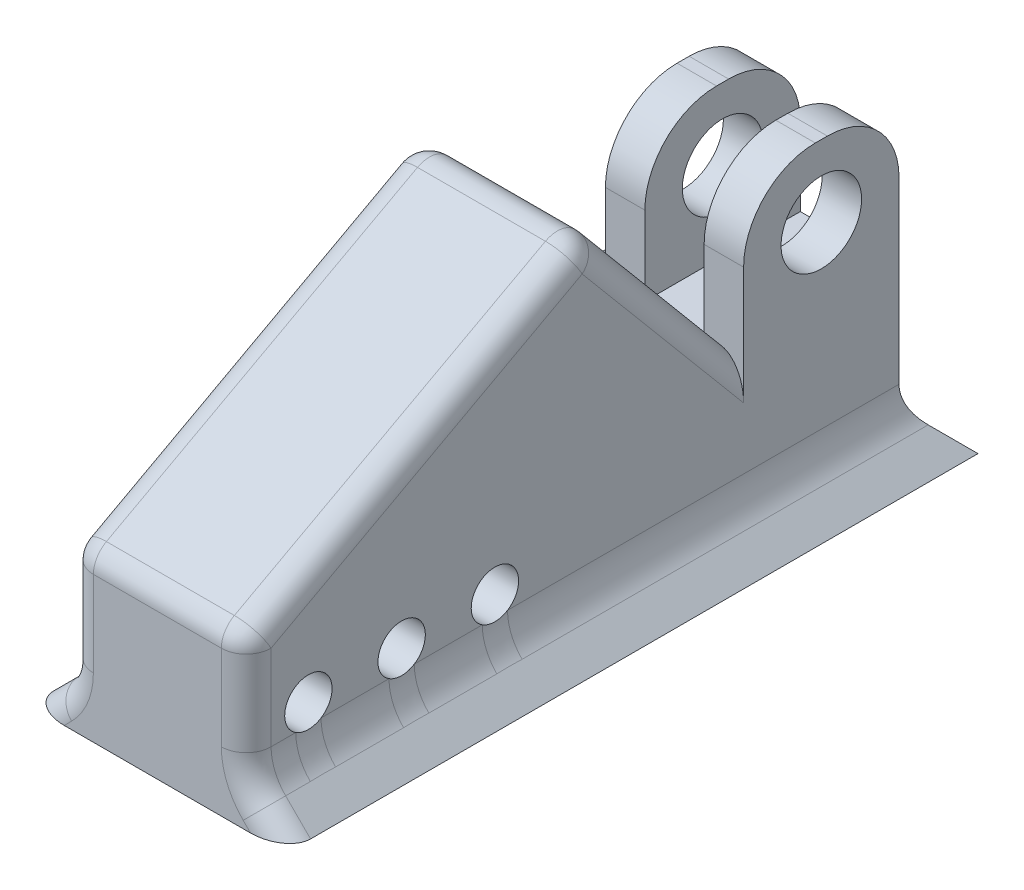
SolidWorks part; units mm, degrees
ref_plane "Front Plane" through (0, 0, 0) normal (0, 0, 1) x (1, 0, 0)
ref_plane "Top Plane" through (0, 0, 0) normal (0, 1, 0) x (1, 0, 0)
ref_plane "Right Plane" through (0, 0, 0) normal (1, 0, 0) x (0, 0, -1)
sketch "Sketch1" plane through (0, 0, 0) normal (0, 0, 1) x (1, 0, 0)
  line L1 (-14.29, -25) -> (14.29, -25)
  line L2 (-14.29, -25) -> (-14.29, 25)
  line L3 (-14.29, 25) -> (14.29, 25)
  line L4 (14.29, -25) -> (14.29, 25)
  line L5 (-14.29, -25) -> (14.29, 25) construction
  line L6 (-14.29, 25) -> (14.29, -25) construction
  point P0 (0, 0)
  dimension "D1" = 50
  dimension "D2" = 28.58
extrude "Boss-Extrude1" add sketch "Sketch1" along normal mid plane 25
sketch "Sketch2" plane through (0, 0, 12.5) normal (0, 0, 1) x (-1, 0, 0)
  line L1 (-7.94, -0.775) -> (1.59, -0.775)
  line L2 (-7.94, -0.775) -> (-7.94, -25)
  line L3 (-7.94, -25) -> (1.59, -25)
  line L4 (1.59, -0.775) -> (1.59, -25)
  line L5 (7.94, -0.775) -> (14.29, -0.775)
  line L6 (7.94, -0.775) -> (7.94, -25)
  line L7 (7.94, -25) -> (14.29, -25)
  line L8 (14.29, -0.775) -> (14.29, -25)
  line L10 (-14.29, -25) -> (14.29, -25) construction
  line L11 (14.29, -25) -> (14.29, 25) construction
  line L12 (-14.29, 25) -> (-14.29, -25) construction
  dimension "D1" = 6.35
  dimension "D2" = 6.35
  dimension "D3" = 24.225
  dimension "D4" = 6.35
extrude "Cut-Extrude1" cut sketch "Sketch2" against normal through all
fillet "Fillet1" radius 11.53 4 edges at (-4.765, 25, -12.5) (-4.765, 25, 12.5) (11.115, 25, 12.5) (11.115, 25, -12.5)
sketch "Sketch3" plane through (14.29, 0, 0) normal (1, 0, 0) x (0, 0, -1)
  line L0 (-11.4063, 13.47) -> (20.1617, 13.47) construction
  line L1 (0, 37.5) -> (0, -49962.5) construction
  line L2 (-0.97, 25) -> (0.97, 25) construction
  circle A0 centre (0, 13.47) radius 6.477
  point P9 (0, 25)
  dimension "D1" = 12.954
extrude "Cut-Extrude2" cut sketch "Sketch3" against normal through all
sketch "Sketch4" plane through (14.29, 0, 0) normal (1, 0, 0) x (0, 0, -1)
  line L0 (-15.659, -25) -> (49984.341, -25) construction
  line L2 (-12.5, -25) -> (12.5, -25) construction
  line L3 (18.85, -25) -> (12.5, -18.65)
  line L4 (12.5, -25) -> (12.5, 13.47) construction
  line L5 (12.5, -18.65) -> (12.5, -25)
  line L6 (12.5, -25) -> (18.85, -25)
  dimension "D1" = 6.35
  dimension "D2" = 45
extrude "Boss-Extrude2" add sketch "Sketch4" against normal up to surface (28.58 mm away) up to face at (-14.29, -12.1125, 0)
sketch "Sketch5" plane through (0, 0, 12.5) normal (0, 0, 1) x (1, 0, 0)
  line L0 (-1.59, 0.775) -> (7.94, 0.775) construction
  line L1 (-14.29, -25) -> (14.29, -25)
  line L2 (-14.29, -25) -> (-14.29, 0.775)
  line L3 (-14.29, 0.775) -> (14.29, 0.775)
  line L4 (14.29, -25) -> (14.29, 0.775)
  line L5 (14.29, -25) -> (14.29, 13.47) construction
extrude "Boss-Extrude3" add sketch "Sketch5" along normal blind 80
sketch "Sketch6" plane through (14.29, 0, 0) normal (1, 0, 0) x (0, 0, -1)
  line L0 (-82.5, 0.775) -> (-82.5, -27.4392) construction
  line L1 (-92.5, -25) -> (-92.5, 0.775) construction
  line L2 (-39.7474, -12.1125) -> (-45.2025, -12.1125) construction
  circle A0 centre (-82.5, -12.1125) radius 3.81
  circle A1 centre (-67.5, -12.1125) radius 3.81
  circle A2 centre (-52.5, -12.1125) radius 3.81
  dimension "D1" = 7.62
  dimension "D2" = 10
  dimension "D3" = 15
  dimension "D4" = 15
extrude "Cut-Extrude3" cut sketch "Sketch6" against normal through all both and the other way through all
sketch "Sketch7" plane through (0, 0, -12.5) normal (0, 0, -1) x (-1, 0, 0)
  line L0 (-14.29, -25) -> (-20.64, -25)
  line L1 (-20.64, -25) -> (-14.29, -18.65)
  line L2 (-14.29, -18.65) -> (-14.29, 13.47) construction
  line L3 (14.29, -25) -> (-14.29, -25) construction
  line L4 (-14.29, -25) -> (-14.29, -18.65) construction
  line L5 (-14.29, -18.65) -> (-14.29, -25)
  dimension "D1" = 45
  dimension "D2" = 6.35
extrude "Boss-Extrude4" add sketch "Sketch7" against normal up to surface and the other way up to surface up to face at (0, -12.1125, 92.5) other way up to face at (0, -21.825, -15.675)
mirror "Mirror2" about plane through (0, 0, 0) normal (1, 0, 0) of "Boss-Extrude4"
hole_wizard "Trous de centrage Ø5.0mm1" positions "Sketch9" profile "Sketch11" hole size "Ø5.0" standard "Ansi Metric"
sketch "Sketch9" plane through (0, -25, 0) normal (0, -1, 0) x (-1, 0, 0)
  point P0 (-7.5, 0.5343)
  point P3 (7.5, 0.5343)
  point P6 (7.5, -14.4657)
  point P9 (-7.5, -14.4657)
  point P12 (-7.5, -29.4657)
  point P14 (7.5, -29.4657)
  point P16 (7.5, -44.4657)
  point P18 (-7.5, -44.4657)
  dimension "D1" = 15
  dimension "D2" = 15
  dimension "D3" = 15
  dimension "D4" = 15
sketch "Sketch11" plane through (7.5, -25, -0.5343) normal (1, 0, 0) x (0, 0, -1)
  line L0 (0, 0) -> (0, 11.5022)
  line L1 (0, 11.5022) -> (2.5, 10)
  line L2 (2.5, 10) -> (2.5, 0)
  line L5 (2.5, 0) -> (0, 0)
  line L10 (0, 11.5022) -> (-2.5, 10) construction
  line L11 (0, -6.35) -> (0, 107.95) construction
  dimension "Hole Dia." = 5
  dimension "Hole Depth" = 10
  dimension "Drill Angle" = 118
sketch "Esquisse1" plane through (14.29, 0, 0) normal (1, 0, 0) x (0, 0, -1)
  line L1 (-37.5, 30.5688) -> (-12.5, 0.775)
  line L2 (-12.5, 0.775) -> (-92.5, 0.775)
  line L5 (-92.5, 0.775) -> (-37.5, 30.5688)
  dimension "D1" = 50
  dimension "D2" = 25
extrude "Boss.-Extru.1" add sketch "Esquisse1" against normal up to surface (28.58 mm away) up to face at (-14.29, -12.1125, 48.69)
fillet "Fillet2" radius 8 3 edges at (-14.29, -18.65, 40) (14.29, -18.65, 40) (0, -18.65, -12.5)
fillet "Fillet4" radius 4 13 edges at (-14.29, 0.775, 0) (-18.6366, -22.9966, 92.5) (-14.899, -18.3978, 92.5) (18.6366, -22.9966, 92.5) (14.899, -18.3978, 92.5) (-14.29, -7.2806, 92.5) (14.29, -7.2806, 92.5) (-14.29, 15.6719, 25) (14.29, 15.6719, 25) (0, 0.775, 92.5) (-14.29, 15.6719, 65) (14.29, 15.6719, 65) (0, 30.5688, 37.5)
